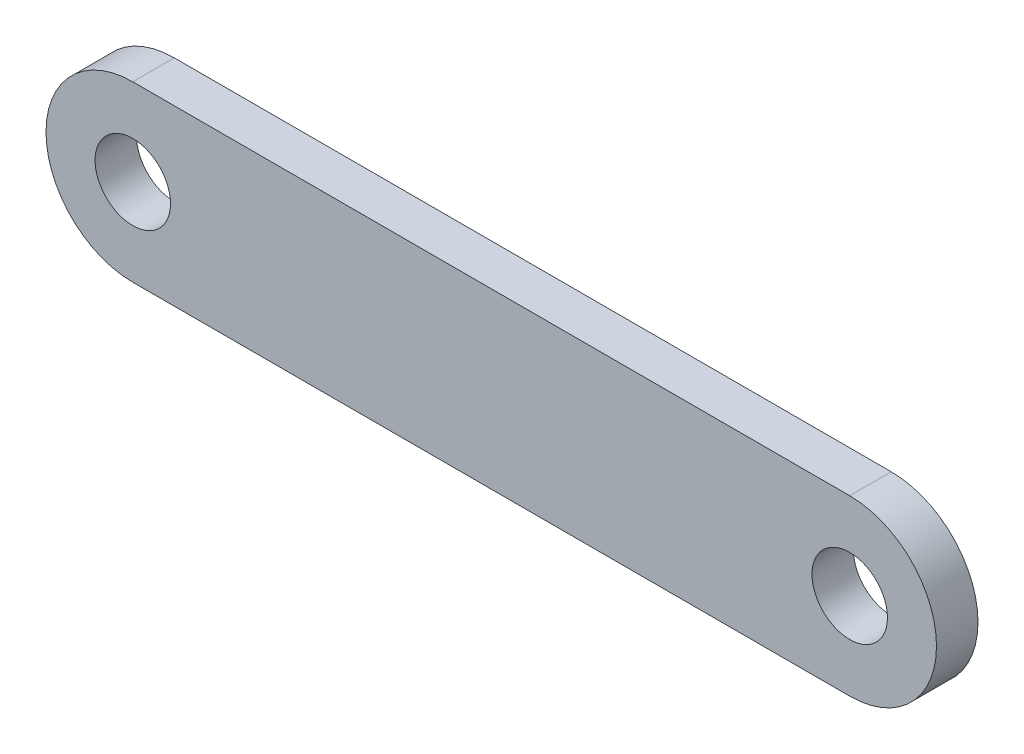
SolidWorks part; units mm, degrees
material "1.0490 (S275N)"
ref_plane "Front Plane" through (0, 0, 0) normal (0, 0, 1) x (1, 0, 0)
ref_plane "Top Plane" through (0, 0, 0) normal (0, 1, 0) x (1, 0, 0)
ref_plane "Right Plane" through (0, 0, 0) normal (1, 0, 0) x (0, 0, -1)
sketch "Sketch1" plane through (0, 0, 0) normal (0, 0, 1) x (1, 0, 0)
  line L0 (-47.5, 0) -> (47.5, 0) construction
  line L1 (-47.5, 11.5) -> (47.5, 11.5)
  line L2 (-47.5, -11.5) -> (47.5, -11.5)
  arc A0 (-47.5, 11.5) -> (-47.5, -11.5) centre (-47.5, 0) ccw
  arc A1 (47.5, -11.5) -> (47.5, 11.5) centre (47.5, 0) ccw
  circle A2 centre (-47.5, 0) radius 5
  circle A3 centre (47.5, 0) radius 5
  point P3 (0, 0)
  dimension "D3" = 47.5
  dimension "D4" = 10
  dimension "D5" = 10
  dimension "D1" = 95
  dimension "D2" = 23
extrude "link_AB" add sketch "Sketch1" along normal mid plane 5.5
